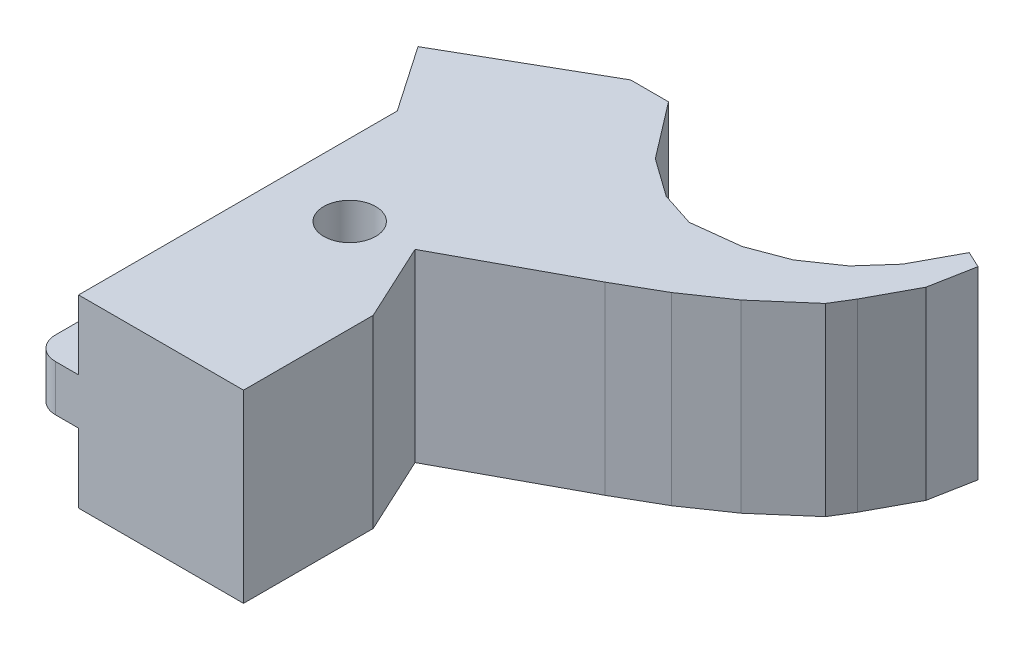
SolidWorks part; units mm, degrees
ref_plane "Front Plane" through (0, 0, 0) normal (0, 0, 1) x (1, 0, 0)
ref_plane "Top Plane" through (0, 0, 0) normal (0, 1, 0) x (1, 0, 0)
ref_plane "Right Plane" through (0, 0, 0) normal (1, 0, 0) x (0, 0, -1)
sketch "Sketch1" plane through (0, 0, 0) normal (0, 1, 0) x (1, 0, 0)
  line L0 (4.2084, 17.2449) -> (8.2084, 17.2449) construction
  line L1 (0, 0) -> (14.2923, 0)
  line L2 (14.2923, 0) -> (14.2923, 11.2386)
  line L3 (14.2923, 11.2386) -> (11.1561, 17.995)
  line L4 (0, 0) -> (0, 27.6127)
  line L5 (0, 27.6127) -> (-3.9278, 33.3369)
  line L6 (-3.9278, 33.3369) -> (7.7799, 40.0491)
  line L7 (7.7799, 40.0491) -> (11.0636, 40.0491)
  line L8 (11.0636, 40.0491) -> (14.769, 35.2028)
  line L9 (14.769, 35.2028) -> (18.052, 32.8631)
  line L10 (18.052, 32.8631) -> (21.0021, 31.9013)
  line L11 (21.0021, 31.9013) -> (25.1093, 32.3822)
  line L12 (25.1093, 32.3822) -> (28.3448, 33.5947)
  line L13 (28.3448, 33.5947) -> (31.2154, 35.5644)
  line L14 (31.2154, 35.5644) -> (33.3859, 38.0038)
  line L15 (33.3859, 38.0038) -> (35.4096, 41.7622)
  line L16 (35.4096, 41.7622) -> (36.8433, 41.0875)
  line L17 (36.8433, 41.0875) -> (36.1265, 37.2924)
  line L18 (36.1265, 37.2924) -> (34.0491, 33.4344)
  line L19 (34.0491, 33.4344) -> (32.9901, 31.711)
  line L20 (32.9901, 31.711) -> (29.0852, 28.3229)
  line L21 (29.0852, 28.3229) -> (25.5178, 25.875)
  line L22 (25.5178, 25.875) -> (21.8356, 23.764)
  line L23 (21.8356, 23.764) -> (11.1561, 17.995)
  circle A0 centre (6.2342, 17.2589) radius 2.25
  dimension "D2" = 4.5
  dimension "D1" = 4
extrude "Boss-Extrude1" add sketch "Sketch1" along normal blind 16
sketch "Sketch4" plane through (0, 0, 0) normal (-1, 0, 0) x (0, 0, 1)
  line L0 (-4, 0) -> (-4, 16) construction
  line L1 (-27.6127, 0) -> (0, 0) construction
  line L2 (-27.6127, 16) -> (0, 16) construction
  line L3 (0, 16) -> (0, 0) construction
  line L4 (-8, 10) -> (0, 10)
  line L5 (-8, 10) -> (-8, 6)
  line L6 (-8, 6) -> (0, 6)
  line L7 (0, 10) -> (0, 6)
  line L8 (-8, 10) -> (0, 6) construction
  line L9 (-8, 6) -> (0, 10) construction
  point P9 (-4, 8)
  dimension "D1" = 4
  dimension "D2" = 4
extrude "Boss-Extrude3" add sketch "Sketch4" along normal blind 4 contours L5 L4 L7 L6
sketch "Sketch5" plane through (0, 10, 0) normal (0, 1, 0) x (1, 0, 0)
  line L0 (-4, 8) -> (0, 8) construction
  line L10 (-2, 8) -> (-2, 4.4509)
  line L11 (-1.5, 3.9509) -> (-0.5, 3.9509)
  line L12 (0, 27.6127) -> (0, 0) construction
  line L13 (0, 4.4509) -> (0, 8)
  line L14 (0, 8) -> (-2, 8)
  line L15 (-4, 2) -> (-4, 0)
  line L16 (-4, 0) -> (-2, 0)
  arc A3 (-1.5, 3.9509) -> (-2, 4.4509) centre (-1.5, 4.4509) cw
  arc A4 (0, 4.4509) -> (-0.5, 3.9509) centre (-0.5, 4.4509) cw
  arc A5 (-4, 2) -> (-2, 0) centre (-2, 2) ccw
  point P13 (0, 3.9509)
  point P22 (-4, 0)
  dimension "D2" = 0.5
  dimension "D3" = 2
  dimension "D1" = 0.5
extrude "Cut-Extrude2" cut sketch "Sketch5" against normal blind 6
